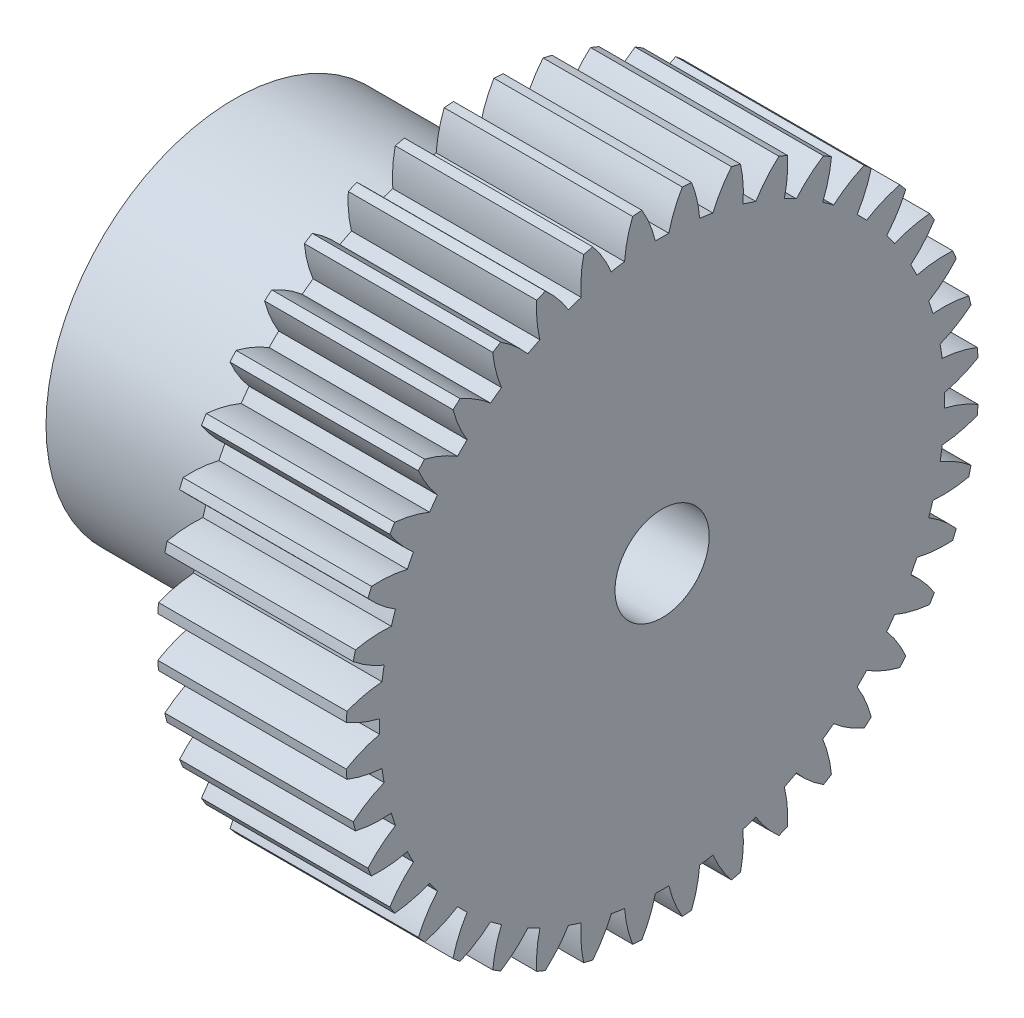
SolidWorks part; units mm, degrees
ref_plane "Plane1" through (0, 0, 0) normal (0, 0, 1) x (1, 0, 0)
ref_plane "Plane2" through (0, 0, 0) normal (0, 1, 0) x (1, 0, 0)
ref_plane "Plane3" through (0, 0, 0) normal (1, 0, 0) x (0, 0, -1)
sketch "HoldingSke" plane through (0, 0, 0) normal (0, 1, 0) x (1, 0, 0)
  line L0 (0, 0) -> (0.9576, -0.8035)
  line L1 (-15, 0) -> (100, 0) construction
  line L2 (0, 0) -> (-2.1039, 2.3779)
  line L3 (0, 0) -> (-11.863, 4.5341)
  line L4 (0, 0) -> (6.6156, 5.5511)
  line L5 (0, 0) -> (-9.3695, -3.4946)
  line L6 (0, 0) -> (-8.2896, -5.593)
  line L7 (-2.1039, 2.3779) -> (0.0486, 12.1435)
  line L8 (-76.2, 54.61) -> (-75.3, 54.61)
  line L9 (-71.009, 38.7566) -> (-53.1078, 45.2721)
  line L10 (-76.2, 71.12) -> (104.1128, 71.12)
  line L11 (0, 0) -> (-10, 0)
  line L12 (-76.2, 101.6) -> (-76.17, 101.6)
  line L13 (24.9733, 27.94) -> (52.9518, 28.4284)
  line L14 (24.9733, 27.94) -> (24.9743, 27.94)
  line L15 (24.9733, 27.94) -> (100.4006, 29.5858)
  line L16 (-63.627, -0.8) -> (-12.827, -0.8)
  circle A0 centre (0, 0) radius 2.5
  circle A1 centre (0, 0) radius 10
  circle A2 centre (0, 0) radius 10
  circle A3 centre (0, 0) radius 2.5
  dimension "MHD" = 20
  dimension "Hub_dia" = 20
  dimension "Bore" = 5
  dimension "MBD" = 5
  dimension "Pitch" = 1.25
  dimension "Overall_len" = 10
  dimension "Thickness" = 10
  dimension "OAL" = 10.0001
  dimension "T_dim" = 0.9
  dimension "Ap" = 20
  dimension "H" = 19.05
  dimension "Pitch_radius" = 180.3128
  dimension "Width" = 10
  dimension "Backlash" = 0.03
  dimension "Addendum_fac" = 1
  dimension "Dedendum_fac" = 1.25
  dimension "Clearance_fac" = 0.25
  dimension "Dedendum_add" = 0.001
  dimension "Module" = 0.8
sketch "BasProSke" plane through (0, 0, 0) normal (0, 1, 0) x (1, 0, 0)
  line L0 (-10, 0) -> (60, 0) construction
  line L1 (0, 0) -> (0, 16.8)
  line L2 (0, 0) -> (10, 0)
  line L3 (10, 0) -> (10, 16.8)
  line L4 (10, 16.8) -> (0, 16.8)
  dimension "Thickness" = 10
revolve "Base-Revolve" add sketch "BasProSke" angle 360 about L0
sketch "TooCutSke" plane through (0, 0, 0) normal (1, 0, 0) x (0, 0, -1)
  line L1 (0, 0) -> (0, 107) construction
  line L2 (0, 0) -> (-0.6807, 15.9855) construction
  line L3 (0, 0) -> (-2.5091, 31.8807) construction
  line L4 (-0.6807, 15.9855) -> (-1.2545, 15.9404) construction
  arc A0 (0.3582, 14.9947) -> (-0.3582, 14.9947) centre (0, 0) ccw
  arc A1 (1.086, 16.7903) -> (-1.086, 16.7903) centre (0, 0) ccw
  circle A2 centre (0, 0) radius 16 construction
  circle A3 centre (0, 0) radius 15.0351 construction
  arc A4 (-0.3582, 14.9947) -> (-1.086, 16.7903) centre (-6.5851, 13.5163) ccw
  arc A5 (1.086, 16.7903) -> (0.3582, 14.9947) centre (6.5851, 13.5163) ccw
  dimension "Half_CT" = 0.5757
extrude "ToothCut" cut sketch "TooCutSke" along normal through all
fillet "Breaks" [suppressed] radius 0.016
fillet "RootFillets" [suppressed] radius 0.201
pattern_circular "TeethCuts" count 40 every 9 about axis through (-10, 0, 0) along (1, 0, 0) of "ToothCut", "RootFillets", "Breaks"
sketch "HubNeaOneSke" plane through (0, 0, 0) normal (-1, 0, 0) x (0, 0, 1)
  circle A0 centre (0, 0) radius 10
  dimension "Diameter" = 20
extrude "HubNearOne" add sketch "HubNeaOneSke" along normal blind 12.7001
sketch "HubNeaBotSke" plane through (0, 0, 0) normal (-1, 0, 0) x (0, 0, 1)
  circle A0 centre (0, 0) radius 10
  dimension "Diameter" = 20
extrude "HubNearBoth" [suppressed] add sketch "HubNeaBotSke" along normal blind 6.35
ref_plane "FarPln" through (10, 0, 0) normal (1, 0, 0) x (0, 0, -1)
sketch "HubFarSke" plane through (10, 0, 0) normal (1, 0, 0) x (0, 0, -1)
  circle A0 centre (0, 0) radius 10
  dimension "Diameter" = 20
extrude "HubFar" [suppressed] add sketch "HubFarSke" along normal blind 6.35
sketch "BorSke" plane through (0, 0, 0) normal (1, 0, 0) x (0, 0, -1)
  circle A0 centre (0, 0) radius 2.5
  dimension "Diameter" = 5
extrude "Bore" cut sketch "BorSke" along normal through all both and the other way through all
sketch "KeySke" plane through (0, 0, 0) normal (1, 0, 0) x (0, 0, -1)
  line L0 (-1, 0) -> (-1, 3.4)
  line L1 (-1, 3.4) -> (1, 3.4)
  line L2 (1, 3.4) -> (1, 0)
  line L3 (0, 0) -> (0, 34) construction
  line L4 (-1, 0) -> (1, 0)
  dimension "Offset" = 3.4
  dimension "Width" = 2
extrude "Keyway" [suppressed] cut sketch "KeySke" along normal mid plane 20.0001
pattern_circular "Keyway2" [suppressed] count 2 every 90 about axis through (-10, 0, 0) along (1, 0, 0)
sketch "Sketch1" plane through (0, 0, 0) normal (0, 1, 0) x (1, 0, 0)
  line L0 (-6.35, -0.2989) -> (-6.35, 4.8047) construction
  line L1 (-12.7001, 10) -> (-12.7001, -10) construction
  line L2 (0, 10) -> (0, -10) construction
  line L3 (-6.35, 0) -> (13.455, 0) construction
  line L4 (-12.7001, -10) -> (0, -10) construction
  line L5 (0, 10) -> (-12.7001, 10) construction
  circle A0 centre (-6.35, 0) radius 2.65
  dimension "D1" = 5.3
extrude "Cut-Extrude1" cut sketch "Sketch1" against normal blind 10
equation "' \"Module@HoldingSke\" = 6.35"
equation "' \"Num_teeth@HoldingSke\" = 12"
equation "' \"Ap@HoldingSke\" =  20"
equation "' \"Ap@HoldingSke\" = 20"
equation "' \"Width@HoldingSke\" = 0.5 * 25.4"
equation "' \"Hub_dia@HoldingSke\"= 1 * 25.4"
equation "' \"Hub_dia@HoldingSke\" = 1 * 25.4"
equation "' \"Overall_len@HoldingSke\" = 1.0 * 25.4"
equation "' \"Bore@HoldingSke\" = 0.75 * 25.4"
equation "' \"T_dim@HoldingSke\" = 0.1 * 25.4"
equation "' \"Width@KeySke\" = 0.25 * 25.4"
equation "' \"Show_teeth@HoldingSke\" = 13"
equation "' \"Backlash@HoldingSke\" = 0.009 * 25.4"
equation "' \"Addendum_fac@HoldingSke\" = 1.0"
equation "' \"Dedendum_fac@HoldingSke\" = 1.25"
equation "' \"Dedendum_add@HoldingSke\" = 0.00005 * 25.4"
equation "' \"Clearance_fac@HoldingSke\" = 0.25"
equation "\"Pitch@HoldingSke\" = 1 / \"Module@HoldingSke\""
equation "\"Overcut_dia@TooCutSke\" = (\"Num_teeth@HoldingSke\" + 2 * \"Addendum_fac@HoldingSke\") / \"Pitch@HoldingSke\" + 0.002 * 25.4"
equation "\"Pitch_dia@TooCutSke\" = \"Num_teeth@HoldingSke\" / \"Pitch@HoldingSke\""
equation "\"Base_dia@TooCutSke\" = \"Num_teeth@HoldingSke\" / \"Pitch@HoldingSke\" * cos((\"Ap@HoldingSke\"  * 3.14159265 / 180))"
equation "\"Root_dia@TooCutSke\" = (\"Num_teeth@HoldingSke\" + 2) / \"Pitch@HoldingSke\" - 2 * (\"Addendum_fac@HoldingSke\" + \"Dedendum_fac@HoldingSke\") / \"Pitch@HoldingSke\" - \"Dedendum_add@HoldingSke\" * 2"
equation "\"Half_ang@TooCutSke\" = 180 / \"Num_teeth@HoldingSke\""
equation "\"Half_CT@TooCutSke\" = \"Num_teeth@HoldingSke\" / \"Pitch@HoldingSke\" * sin((3.14159265 / 2 / \"Num_teeth@HoldingSke\")) / 2 - 7 * \"Backlash@HoldingSke\" / 4"
equation "\"Flank_rad@TooCutSke\" = \"Num_teeth@HoldingSke\" / \"Pitch@HoldingSke\" / 5"
equation "\"Radius@RootFillets\" = \"Clearance_fac@HoldingSke\" / \"Pitch@HoldingSke\" + \"Dedendum_add@HoldingSke\""
equation "\"Break_rad@Breaks\" = 0.02 / \"Pitch@HoldingSke\""
equation "\"Thickness@HoldingSke\" = \"Width@HoldingSke\""
equation "\"OAL@HoldingSke\" = \"Thickness@HoldingSke\""
equation "\"MHD@HoldingSke\" = (\"Num_teeth@HoldingSke\" + 2) / \"Pitch@HoldingSke\" - 2 * (\"Addendum_fac@HoldingSke\" + \"Dedendum_fac@HoldingSke\")  / \"Pitch@HoldingSke\" - \"Dedendum_add@HoldingSke\" * 2"
equation "\"MBD@HoldingSke\" = (\"Num_teeth@HoldingSke\" + 2) / \"Pitch@HoldingSke\" - 2 * (\"Addendum_fac@HoldingSke\" + \"Dedendum_fac@HoldingSke\")  / \"Pitch@HoldingSke\" - \"Dedendum_add@HoldingSke\" * 2 - 0.002 * 25.4"
equation "\"MHD@HoldingSke\" = ((sgn( \"MHD@HoldingSke\" - \"Hub_dia@HoldingSke\" )-1)*( \"MHD@HoldingSke\" - \"Hub_dia@HoldingSke\" ))/-2+ \"Hub_dia@HoldingSke\""
equation "\"MBD@HoldingSke\" = ((sgn( \"MBD@HoldingSke\" - \"Bore@HoldingSke\" )-1)*( \"MBD@HoldingSke\" - \"Bore@HoldingSke\" ))/-2+ \"Bore@HoldingSke\""
equation "\"OAL@HoldingSke\" = ((sgn( \"OAL@HoldingSke\" - \"Overall_len@HoldingSke\" )+1)*( \"OAL@HoldingSke\" - \"Overall_len@HoldingSke\" ))/2 + \"Overall_len@HoldingSke\" + 0.000002 * 25.4"
equation "\"Num_teeth@TeethCuts\" = int( \"Show_teeth@HoldingSke\" ) + 1"
equation "\"Num_teeth@TeethCuts\" = ((sgn( \"Num_teeth@TeethCuts\" - \"Num_teeth@HoldingSke\" )-1)*( \"Num_teeth@TeethCuts\" - \"Num_teeth@HoldingSke\" ))/-2+ \"Num_teeth@HoldingSke\""
equation "\"Num_teeth@TeethCuts\" = ((sgn( \"Num_teeth@TeethCuts\" - 2.0)+1)*( \"Num_teeth@TeethCuts\" - 2.0))/2 +2.0"
equation "\"Angle@TeethCuts\" = 360.0 / \"Num_teeth@HoldingSke\""
equation "\"Diameter@BasProSke\" = (\"Num_teeth@HoldingSke\" + 2 * \"Addendum_fac@HoldingSke\") / \"Pitch@HoldingSke\""
equation "\"Thickness@BasProSke\"  = \"Thickness@HoldingSke\""
equation "' \"Fillet_rad@BasProSke\" =  \"Thickness@HoldingSke\" * 0.05"
equation "' \"Fillet_rad@BasProSke\" = \"Thickness@HoldingSke\" * 0.05"
equation "\"MHD@HoldingSke\" = ((sgn( \"MHD@HoldingSke\" - \"Root_dia@TooCutSke\" )-1)*( \"MHD@HoldingSke\" - \"Root_dia@TooCutSke\" ))/-2+ \"Root_dia@TooCutSke\""
equation "\"Diameter@HubNeaOneSke\" = \"MHD@HoldingSke\""
equation "\"Length@HubNearOne\" = \"OAL@HoldingSke\" - \"Thickness@BasProSke\""
equation "\"Diameter@HubNeaBotSke\" = \"MHD@HoldingSke\""
equation "\"Length@HubNearBoth\" = ( \"OAL@HoldingSke\" - \"Thickness@BasProSke\" ) / 2.0"
equation "\"Thickness@FarPln\" = \"Thickness@BasProSke\""
equation "\"Diameter@HubFarSke\" = \"MHD@HoldingSke\""
equation "\"Length@HubFar\" = ( \"OAL@HoldingSke\" - \"Thickness@BasProSke\" ) / 2.0"
equation "\"Diameter@BorSke\" = \"MBD@HoldingSke\""
equation "\"D1@Keyway\" = \"OAL@HoldingSke\" * 2.0"
equation "\"Offset@KeySke\" = \"T_dim@HoldingSke\" + \"MBD@HoldingSke\" / 2.0"
